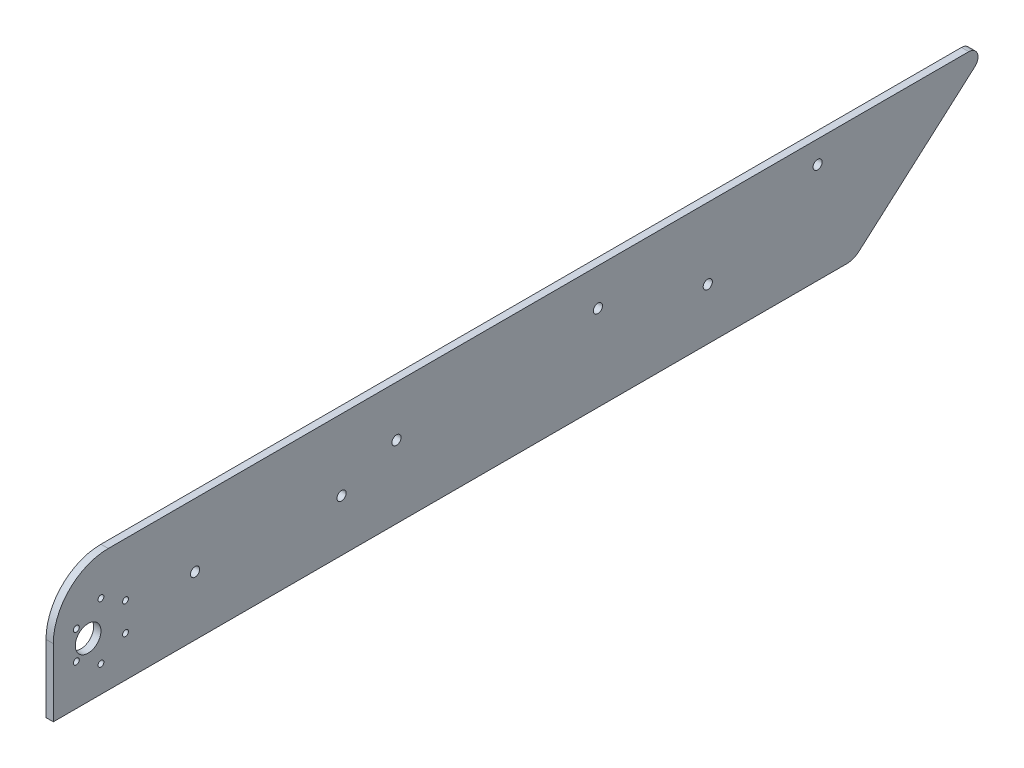
SolidWorks part; units mm, degrees
ref_plane "前视基准面" through (0, 0, 0) normal (0, 0, 1) x (1, 0, 0)
ref_plane "上视基准面" through (0, 0, 0) normal (0, 1, 0) x (1, 0, 0)
ref_plane "右视基准面" through (0, 0, 0) normal (1, 0, 0) x (0, 0, -1)
sketch "草图1" plane through (0, 0, 0) normal (-1, 0, 0) x (0, 0, 1)
  line L0 (-206.9438, -7) -> (226.4067, -7)
  line L160 (226.4067, 60) -> (226.4067, -7)
  line L161 (226.4067, 60) -> (-273.5933, 60)
  line L162 (-276.8968, 51.2467) -> (-213.5507, -4.5066)
  arc A0 (-213.5507, -4.5066) -> (-206.9438, -7) centre (-206.9438, 3) ccw
  circle A4 centre (-191.0077, 47.8481) radius 2.5
  circle A5 centre (68.9923, 21.2334) radius 2.5
  circle A7 centre (38.9923, 32.5499) radius 2.5
  circle A11 centre (-131.0077, 21.2334) radius 2.5
  circle A12 centre (207.4067, 23.0069) radius 7
  circle A13 centre (148.9923, 25.2334) radius 2.5
  circle A14 centre (-71.0077, 39.8664) radius 2.5
  circle A28 centre (213.8301, 30.7569) radius 1.6
  circle A29 centre (200.4067, 38.5069) radius 1.6
  circle A30 centre (186.9833, 30.7569) radius 1.6
  circle A31 centre (186.9833, 15.2569) radius 1.6
  circle A32 centre (200.4067, 7.5069) radius 1.6
  circle A33 centre (213.8301, 15.2569) radius 1.6
  arc A525 (-273.5933, 60) -> (-276.8968, 51.2467) centre (-273.5933, 55) ccw
  point P0 (-150, 0)
  point P1 (135, 0)
  point P9 (-344.9533, 138.7825)
  point P10 (187.1329, 101.1747)
  point P11 (165.9429, -19)
  point P12 (-156.9154, -19)
  dimension "D1" = 10
extrude "凸台-拉伸1" add sketch "草图1" along normal blind 4
fillet "圆角1" radius 30 1 edges at (-2, 60, 226.4067)
